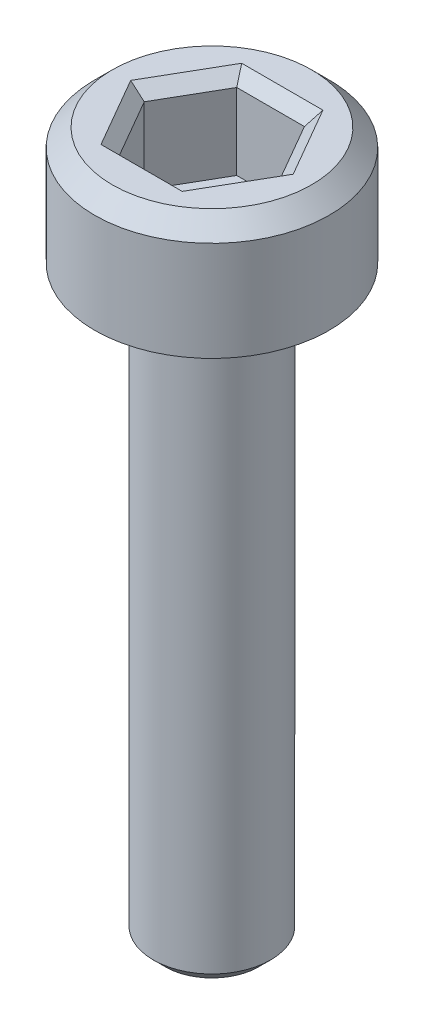
SolidWorks part; units mm, degrees
ref_plane "Front Plane" through (0, 0, 0) normal (0, 0, 1) x (1, 0, 0)
ref_plane "Top Plane" through (0, 0, 0) normal (0, 1, 0) x (1, 0, 0)
ref_plane "Right Plane" through (0, 0, 0) normal (1, 0, 0) x (0, 0, -1)
sketch "Sketch1" plane through (0, 0, 0) normal (0, 1, 0) x (1, 0, 0)
  circle A0 centre (0, 0) radius 2
  dimension "D1" = 4
extrude "Boss-Extrude1" add sketch "Sketch1" along normal blind 2
chamfer "Chamfer1" distance 0.3 angle 45 1 edges at (0, 2, 2)
sketch "Sketch2" plane through (0, 2, 0) normal (0, 1, 0) x (1, 0, 0)
  line L1 (1.1547, 0) -> (0.5774, 1)
  line L2 (0.5774, 1) -> (-0.5774, 1)
  line L3 (-0.5774, 1) -> (-1.1547, 0)
  line L4 (-1.1547, 0) -> (-0.5774, -1)
  line L5 (-0.5774, -1) -> (0.5774, -1)
  line L6 (0.5774, -1) -> (1.1547, 0)
  circle A0 centre (0, 0) radius 1 construction
  dimension "D1" = 2
extrude "Cut-Extrude1" cut sketch "Sketch2" against normal blind 1.5
chamfer "Chamfer2" distance 0.2 angle 45 6 edges at (0.866, 2, -0.5) (0.866, 2, 0.5) (0, 2, 1) (-0.866, 2, 0.5) (-0.866, 2, -0.5) (0, 2, -1)
sketch "Sketch3" plane through (0, 0, 0) normal (0, -1, 0) x (1, 0, 0)
  circle A0 centre (0, 0) radius 1
  dimension "D1" = 2
extrude "Boss-Extrude2" add sketch "Sketch3" along normal blind 10
chamfer "Chamfer3" distance 0.2 angle 45 1 edges at (0, -10, -1)
